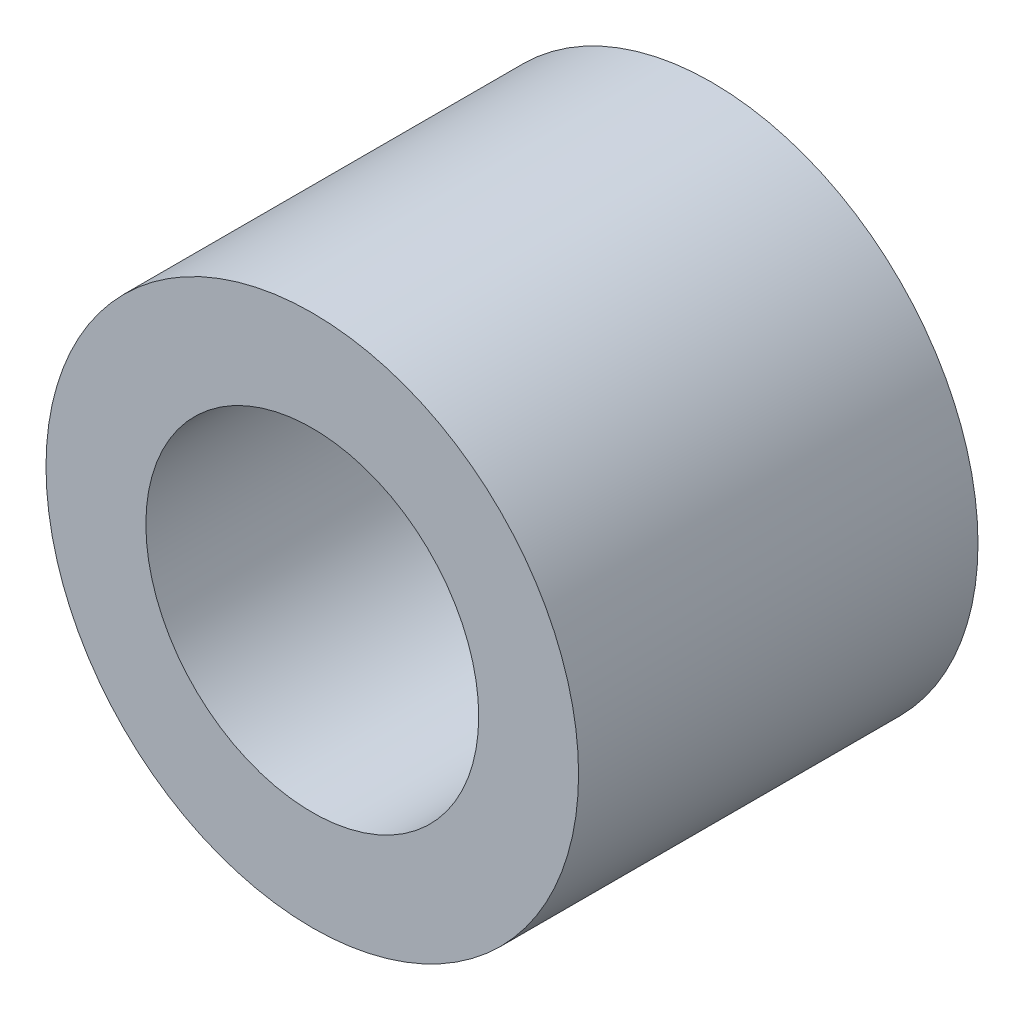
SolidWorks part; units mm, degrees
ref_plane "前视基准面" through (0, 0, 0) normal (0, 0, 1) x (1, 0, 0)
ref_plane "上视基准面" through (0, 0, 0) normal (0, 1, 0) x (1, 0, 0)
ref_plane "右视基准面" through (0, 0, 0) normal (1, 0, 0) x (0, 0, -1)
sketch "草图1" plane through (0, 0, 0) normal (0, 0, 1) x (1, 0, 0)
  circle A0 centre (0, 0) radius 5
  circle A1 centre (0, 0) radius 8
  dimension "D1" = 10
  dimension "D2" = 16
extrude "凸台-拉伸1" add sketch "草图1" along normal blind 12
